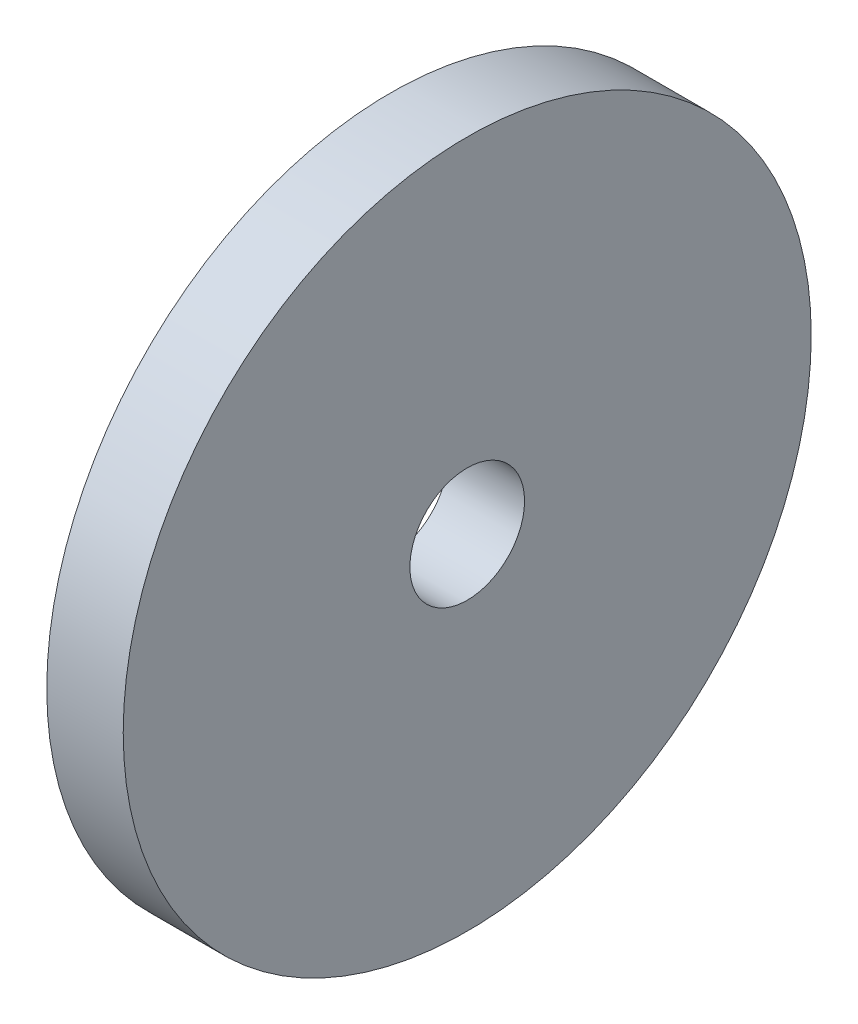
SolidWorks part; units mm, degrees
material "Pine"
ref_plane "Front Plane" through (0, 0, 0) normal (0, 0, 1) x (1, 0, 0)
ref_plane "Top Plane" through (0, 0, 0) normal (0, 1, 0) x (1, 0, 0)
ref_plane "Right Plane" through (0, 0, 0) normal (1, 0, 0) x (0, 0, -1)
sketch "Sketch1" plane through (0, 0, 0) normal (1, 0, 0) x (0, 0, -1)
  circle A0 centre (0, 0) radius 9
  dimension "D1" = 18
extrude "Boss-Extrude1" add sketch "Sketch1" along normal blind 2
sketch "Sketch2" plane through (2, 0, 0) normal (1, 0, 0) x (0, 0, -1)
  circle A2 centre (0, 0) radius 1.5
  dimension "D1" = 3
extrude "Cut-Extrude1" cut sketch "Sketch2" against normal through all
